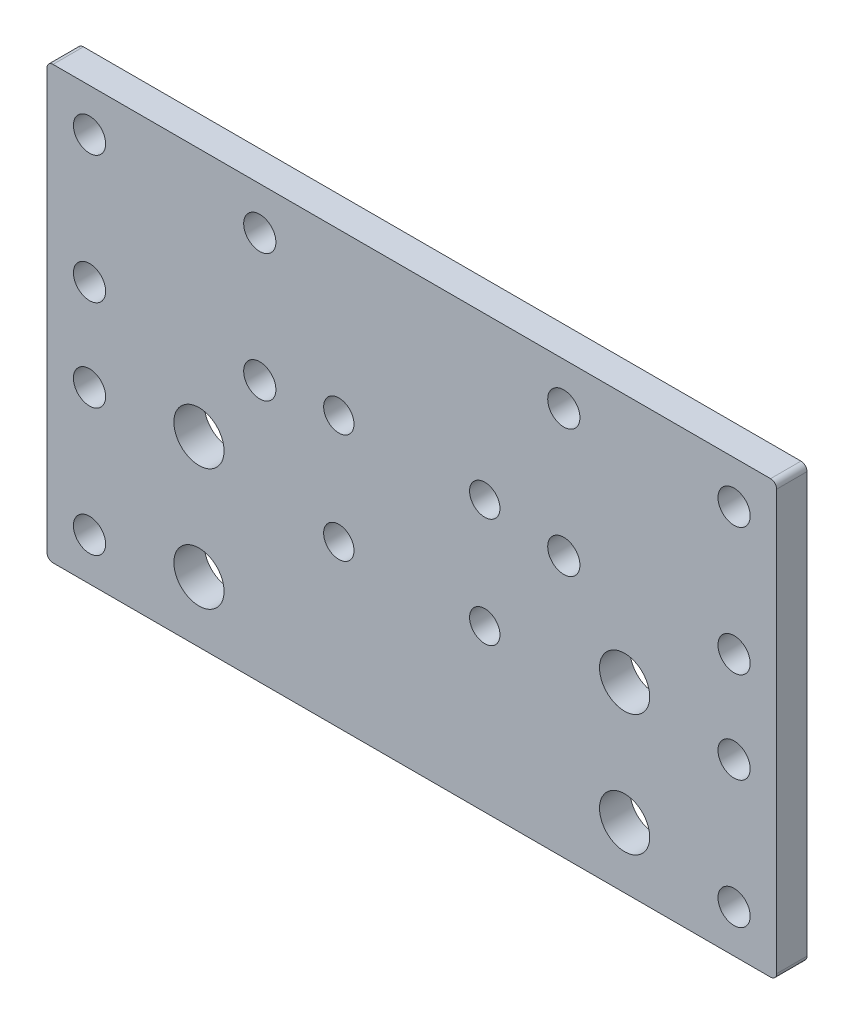
SolidWorks part; units mm, degrees
ref_plane "Front Plane" through (0, 0, 0) normal (0, 0, 1) x (1, 0, 0)
ref_plane "Top Plane" through (0, 0, 0) normal (0, 1, 0) x (1, 0, 0)
ref_plane "Right Plane" through (0, 0, 0) normal (1, 0, 0) x (0, 0, -1)
sketch "Sketch1" plane through (0, 0, 0) normal (0, 0, 1) x (1, 0, 0)
  line L1 (0, 0) -> (120, 0)
  line L2 (0, 0) -> (0, 71)
  line L3 (0, 71) -> (120, 71)
  line L4 (120, 0) -> (120, 71)
  circle A0 centre (48, 44.5) radius 2.5
  circle A1 centre (72, 44.5) radius 2.5
  circle A2 centre (48, 26.5) radius 2.5
  circle A3 centre (72, 26.5) radius 2.5
extrude "Boss-Extrude1" add sketch "Sketch1" along normal blind 5
fillet "Fillet1" radius 1 4 edges at (0, 0, 2.5) (120, 0, 2.5) (120, 71, 2.5) (0, 71, 2.5)
sketch "Sketch3" plane through (0, 0, 0) normal (0, 0, -1) x (-1, 0, 0)
  circle A0 centre (-113, 64) radius 2.65
  circle A1 centre (-113, 43) radius 2.65
  circle A2 centre (-85, 64) radius 2.65
  circle A5 centre (-113, 28) radius 2.65
  circle A7 centre (-113, 7) radius 2.65
  circle A8 centre (-7, 7) radius 2.65
  circle A11 centre (-7, 28) radius 2.65
  circle A12 centre (-7, 64) radius 2.65
  circle A13 centre (-7, 43) radius 2.65
  circle A15 centre (-35, 64) radius 2.65
  circle A16 centre (-35, 43) radius 2.65
  circle A25 centre (-85, 43) radius 2.65
  circle A26 centre (-25, 30) radius 4.1275
  circle A27 centre (-25, 10) radius 4.1275
  circle A28 centre (-95, 10) radius 4.1275
  circle A29 centre (-95, 30) radius 4.1275
extrude "Cut-Extrude1" cut sketch "Sketch3" along normal blind 39 and the other way blind 46
